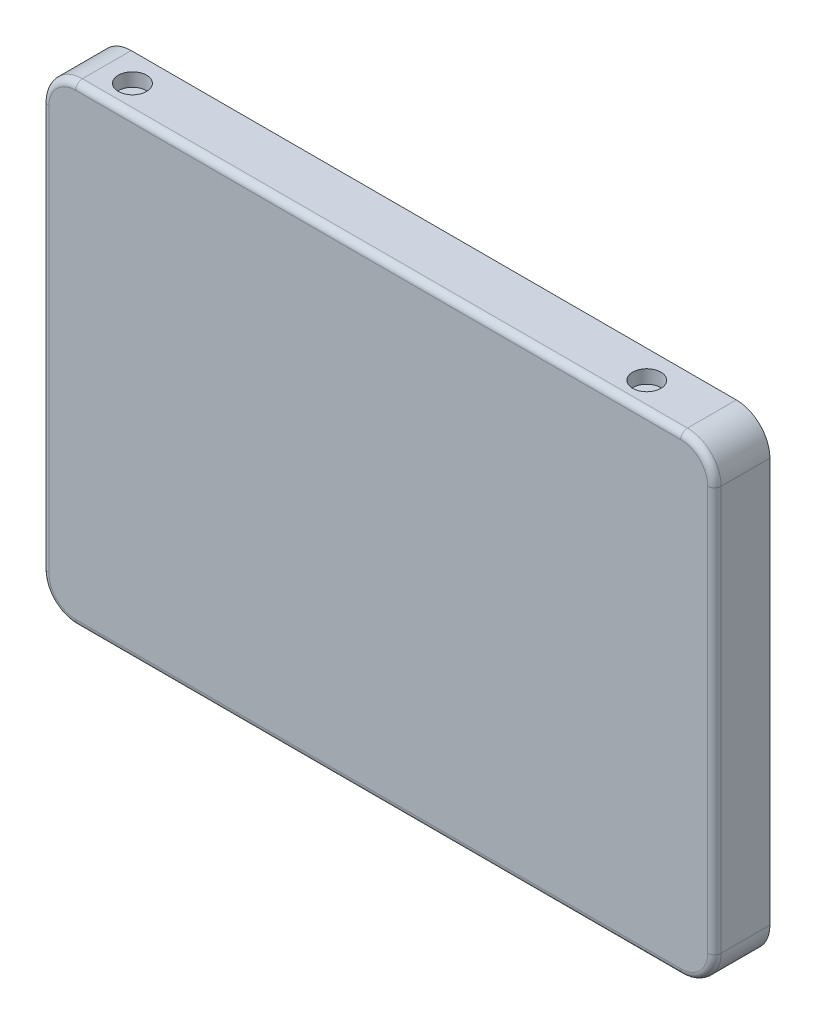
SolidWorks part; units mm, degrees
ref_plane "Front Plane" through (0, 0, 0) normal (0, 0, 1) x (1, 0, 0)
ref_plane "Top Plane" through (0, 0, 0) normal (0, 1, 0) x (1, 0, 0)
ref_plane "Right Plane" through (0, 0, 0) normal (1, 0, 0) x (0, 0, -1)
sketch "Sketch2" plane through (0, 0, 0) normal (0, 0, 1) x (1, 0, 0)
  line L0 (0, -55) -> (0, 55) construction
  line L1 (0, 35.075) -> (100, 35.075)
  line L2 (0, 35.075) -> (0, -35.075)
  line L3 (0, -35.075) -> (100, -35.075)
  line L4 (100, 35.075) -> (100, -35.075)
  line L5 (55, 0) -> (-55, 0) construction
  point P6 (0, 0)
  dimension "D1" = 70.15
  dimension "D2" = 100
extrude "Boss-Extrude1" add sketch "Sketch2" along normal blind 8.25 contours L1 L4 L3 L2
fillet "Fillet1" radius 5 4 edges at (100, -35.075, 4.125) (0, -35.075, 4.125) (100, 35.075, 4.125) (0, 35.075, 4.125)
sketch "Sketch3" plane through (0, 0, 0) normal (0, 1, 0) x (1, 0, 0)
  line L0 (9.31, -4.125) -> (85.81, -4.125) construction
  line L1 (-38.5825, 0) -> (38.5825, 0) construction
  line L2 (9.31, -4.125) -> (5, -4.125) construction
  line L3 (5, -8.25) -> (5, 0) construction
  line L4 (0, -4.5375) -> (0, 4.5375) construction
  circle A0 centre (9.31, -4.125) radius 2.1
  circle A1 centre (85.81, -4.125) radius 2.1
  point P11 (47.56, -4.125)
  dimension "D1" = 4.2
  dimension "D2" = 9.31
  dimension "D3" = 76.5
extrude "Cut-Extrude1" cut sketch "Sketch3" along normal blind 2 from surface at -35.075 contours A0 | A1 starting at face at (50, -35.075, 4.125)
mirror "Mirror1" about plane through (0, 0, 0) normal (0, 1, 0) of "Cut-Extrude1"
fillet "Fillet2" radius 1 8 edges at (1.4645, 33.6105, 8.25) (0, 0, 8.25) (1.4645, -33.6105, 8.25) (50, -35.075, 8.25) (98.5355, -33.6105, 8.25) (100, 0, 8.25) (98.5355, 33.6105, 8.25) (50, 35.075, 8.25)
sketch "Sketch4" plane through (0, 0, 0) normal (0, 0, 1) x (1, 0, 0)
  line L1 (9.31, -30.925) -> (9.31, 30.925) construction
  line L2 (5, -35.075) -> (95, -35.075) construction
  circle A0 centre (9.31, -30.925) radius 2
  circle A1 centre (9.31, 30.925) radius 2
  dimension "D1" = 4
  dimension "D2" = 4.15
ref_plane "Plane1" through (47.56, 0, 0) normal (1, 0, 0) x (0, 0, -1)
extrude "Cut-Extrude2" cut sketch "Sketch4" along normal blind 2 contours A0 | A1
mirror "Mirror2" about plane through (47.56, 0, 0) normal (1, 0, 0) of "Cut-Extrude2"
